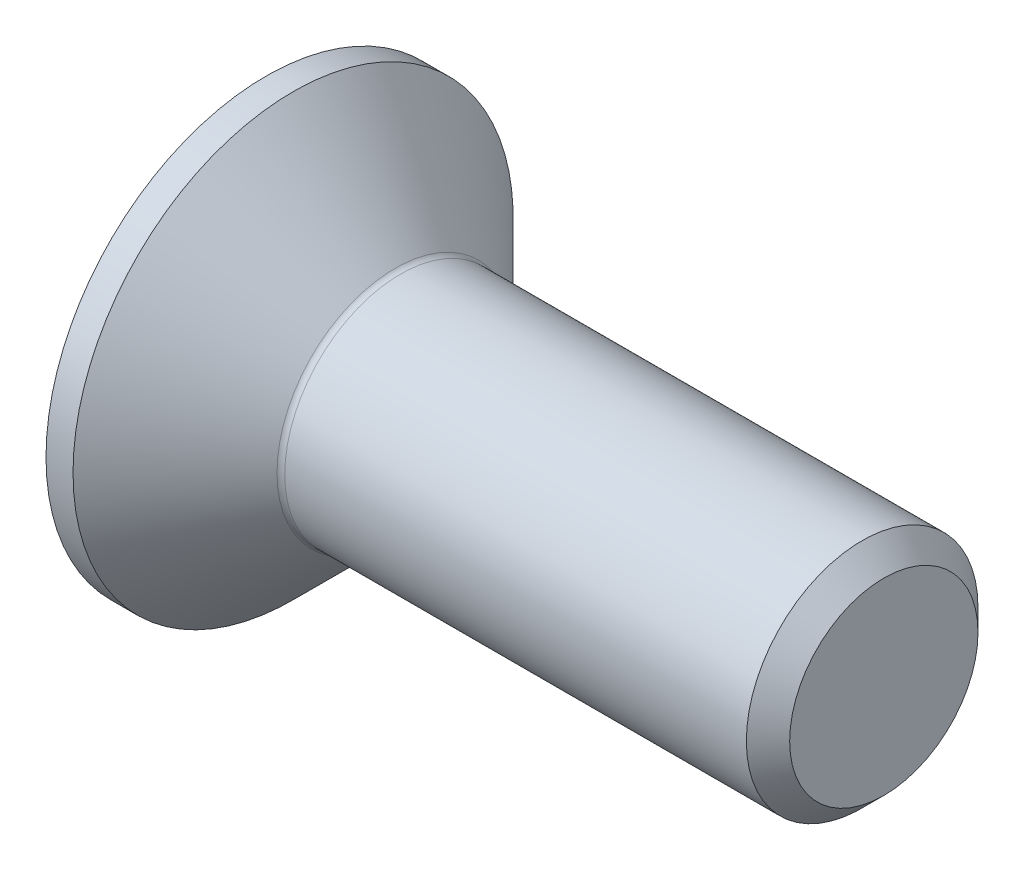
SolidWorks part; units mm, degrees
ref_plane "Plane1" through (0, 0, 0) normal (0, 0, 1) x (1, 0, 0)
ref_plane "Plane2" through (0, 0, 0) normal (0, 1, 0) x (1, 0, 0)
ref_plane "Plane3" through (0, 0, 0) normal (1, 0, 0) x (0, 0, -1)
sketch "BodySke" plane through (0, 0, 0) normal (0, 0, 1) x (1, 0, 0)
  line L0 (0, 0) -> (0, 2.85)
  line L1 (0.35, 2.85) -> (1.7, 1.5)
  line L2 (0, 2.85) -> (0.35, 2.85)
  line L3 (1.7, 1.5) -> (7.7195, 1.5)
  line L4 (8, 1.2195) -> (8, 0)
  line L5 (8, 0) -> (0, 0)
  line L6 (0, 0) -> (127, 0) construction
  line L7 (0.35, -2.85) -> (1.7, -1.5) construction
  line L8 (8, 1.2195) -> (7.7195, 1.5)
  line L9 (0, -2.85) -> (0.35, -2.85) construction
  line L10 (8, -1.2195) -> (7.7195, -1.5) construction
  line L11 (2.2, 7.85) -> (2.2, -14.375) construction
  line L12 (3.2, 16.35) -> (3.2, -5.875) construction
  dimension "Diameter" = 3
  dimension "Head_ht" = 1.7
  dimension "Length" = 8
  dimension "Body_ch_ang" = 45
  dimension "Head_dia" = 5.7
  dimension "Minor_dia" = 2.439
  dimension "Head_ang" = 90
  dimension "Advance" = 0.5
  dimension "Thread_nom" = 4.8
revolve "BaseBody" add sketch "BodySke" angle 360 about L6
cosmetic thread "ThreadCosmetic" parameters "Thread_length"=4.8, "Thread_minor"=2.439
fillet "Fillet1" radius 0.1 1 edges at (1.7, 0, 1.5)
sketch "Sketch2" plane through (0, 0, 0) normal (0, 0, 1) x (1, 0, 0)
  line L0 (0, 1.01) -> (1.2, 1.01)
  line L1 (1.2, 1.01) -> (1.7831, 0)
  line L2 (0, 0) -> (127, 0) construction
  line L3 (1.7831, 0) -> (0, 0)
  line L4 (0, 0) -> (0, 1.01)
  line L5 (0, -1.01) -> (1.2, -1.01) construction
  line L6 (0, 0) -> (47.625, 0) construction
  line L8 (0, 2.85) -> (0, -2.85) construction
  dimension "D2" = 60
  dimension "PreBroach_depth" = 1.2
  dimension "PreBroach_dia" = 2.02
revolve "PreBroach" cut sketch "Sketch2" angle 360 about L6
sketch "Sketch3" plane through (0, 0, 0) normal (-1, 0, 0) x (0, 0, 1)
  line L0 (-1.01, -0.5831) -> (-1.01, 0.5831)
  line L1 (-1.01, 0.5831) -> (0, 1.1662)
  line L2 (0, 1.1662) -> (1.01, 0.5831)
  line L3 (1.01, 0.5831) -> (1.01, -0.5831)
  line L4 (1.01, -0.5831) -> (0, -1.1662)
  line L5 (0, -1.1662) -> (-1.01, -0.5831)
  dimension "D1" = 1.01
  dimension "D2" = 1.01
  dimension "D3" = 2.02
  dimension "Hex_size" = 2.02
extrude "Hex" cut sketch "Sketch3" against normal blind 1.2
sketch "ThdSchSke" plane through (0, 0, 0) normal (0, 0, 1) x (1, 0, 0)
  line L0 (3.2, -1.2195) -> (3.0036, -1.5)
  line L1 (3.2, -1.2195) -> (3.3964, -1.5)
  line L2 (3.3964, -1.5) -> (3.3964, -1.875)
  line L3 (-3.175, 0) -> (5.1513, 0) construction
  line L4 (0, 2.85) -> (0, -2.85) construction
  line L5 (3.3964, -1.875) -> (3.0036, -1.875)
  line L6 (3.0036, -1.875) -> (3.0036, -1.5)
  dimension "Thread_minor" = 2.439
  dimension "Diameter" = 3
  dimension "Start" = 3.2
  dimension "SideAngle" = 55
  dimension "VeeAngle" = 70
  dimension "Overcut" = 3.75
revolve "ThreadSchematic" [suppressed] cut sketch "ThdSchSke" angle 360 about L3
pattern_linear "ThdSchPat" [suppressed]
equation "\"Thread_minor@ThreadCosmetic\"  =  \"Minor_dia@BodySke\""
equation "\"D1@Sketch3\" = \"Hex_size@Sketch3\" / 2"
equation "\"D2@Sketch3\" = \"D1@Sketch3\""
equation "\"D3@Sketch3\" = \"Hex_size@Sketch3\""
equation "\"Thread_length@ThreadCosmetic\" = ((sgn( (\"Length@BodySke\" - \"Advance@BodySke\" * 1.5 - \"Head_ht@BodySke\" ) - \"Thread_nom@BodySke\" )-1)*( (\"Length@BodySke\" - \"Advance@BodySke\" * 1.5 - \"Head_ht@BodySke\" ) - \"Thread_nom@BodySke\" ))/-2+ \"Thread_nom@BodySke\""
equation "\"Thread_minor@ThdSchSke\" = \"Minor_dia@BodySke\""
equation "\"Diameter@ThdSchSke\" = \"Diameter@BodySke\""
equation "\"Overcut@ThdSchSke\" = \"Diameter@BodySke\" * 1.25"
equation "\"Start@ThdSchSke\" = 0.000001 + \"Length@BodySke\" - \"Thread_length@ThreadCosmetic\"  '---Countersunk---"
equation "\"Num_threads@ThdSchPat\" = int( \"Thread_length@ThreadCosmetic\" / \"Advance@BodySke\" + 0.999 )  + 1"
equation "\"Advance@ThdSchPat\" = \"Thread_length@ThreadCosmetic\" /  (\"Num_threads@ThdSchPat\" - 1) 'relax it"
equation "\"Num_threads@ThdSchPat\" = \"Num_threads@ThdSchPat\" - sgn( \"Num_threads@ThdSchPat\" - 1) '---chamfered tips only---"
